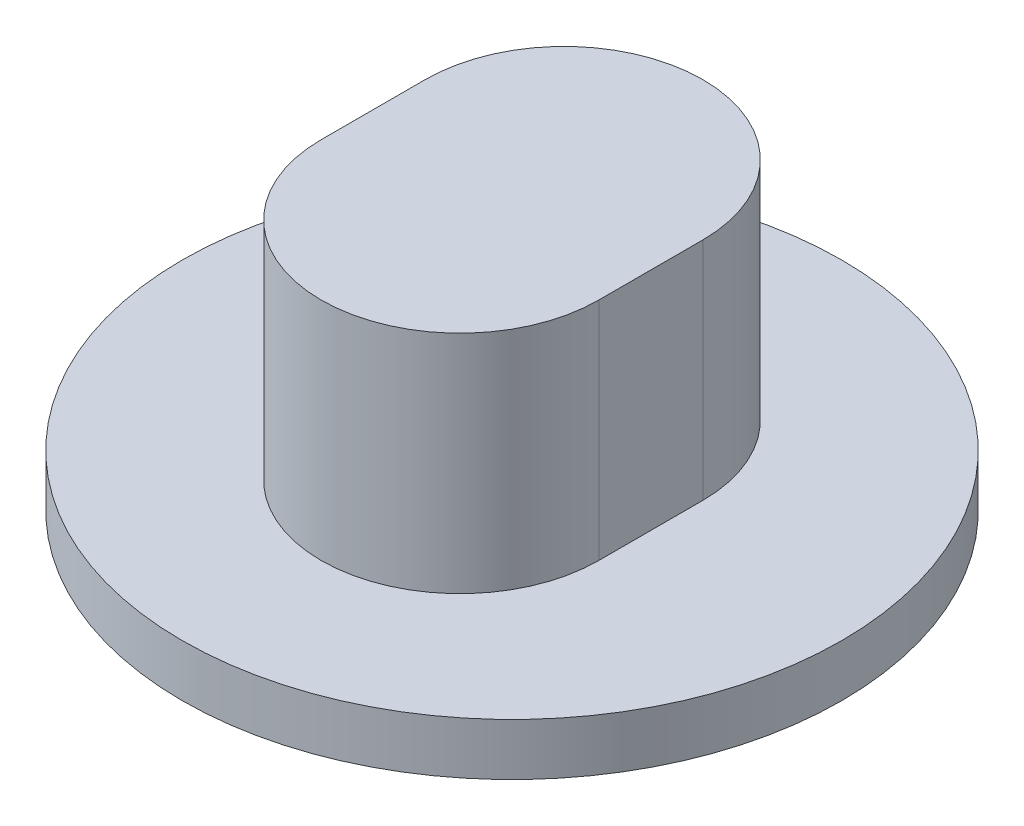
SolidWorks part; units mm, degrees
ref_plane "Front Plane" through (0, 0, 0) normal (0, 0, 1) x (1, 0, 0)
ref_plane "Top Plane" through (0, 0, 0) normal (0, 1, 0) x (1, 0, 0)
ref_plane "Right Plane" through (0, 0, 0) normal (1, 0, 0) x (0, 0, -1)
sketch "Sketch1" plane through (0, 0, 0) normal (0, 1, 0) x (1, 0, 0)
  circle A0 centre (0, 0) radius 19
  dimension "D1" = 38
extrude "Boss-Extrude1" add sketch "Sketch1" along normal blind 3
sketch "Sketch2" plane through (0, 3, 0) normal (0, 1, 0) x (1, 0, 0)
  line L0 (0, -3) -> (0, 3) construction
  line L1 (-8, -3) -> (-8, 3)
  line L2 (8, -3) -> (8, 3)
  arc A0 (-8, -3) -> (8, -3) centre (0, -3) ccw
  arc A1 (8, 3) -> (-8, 3) centre (0, 3) ccw
  point P2 (0, 0)
  dimension "D1" = 22
  dimension "D2" = 16
extrude "Boss-Extrude2" add sketch "Sketch2" along normal blind 13
